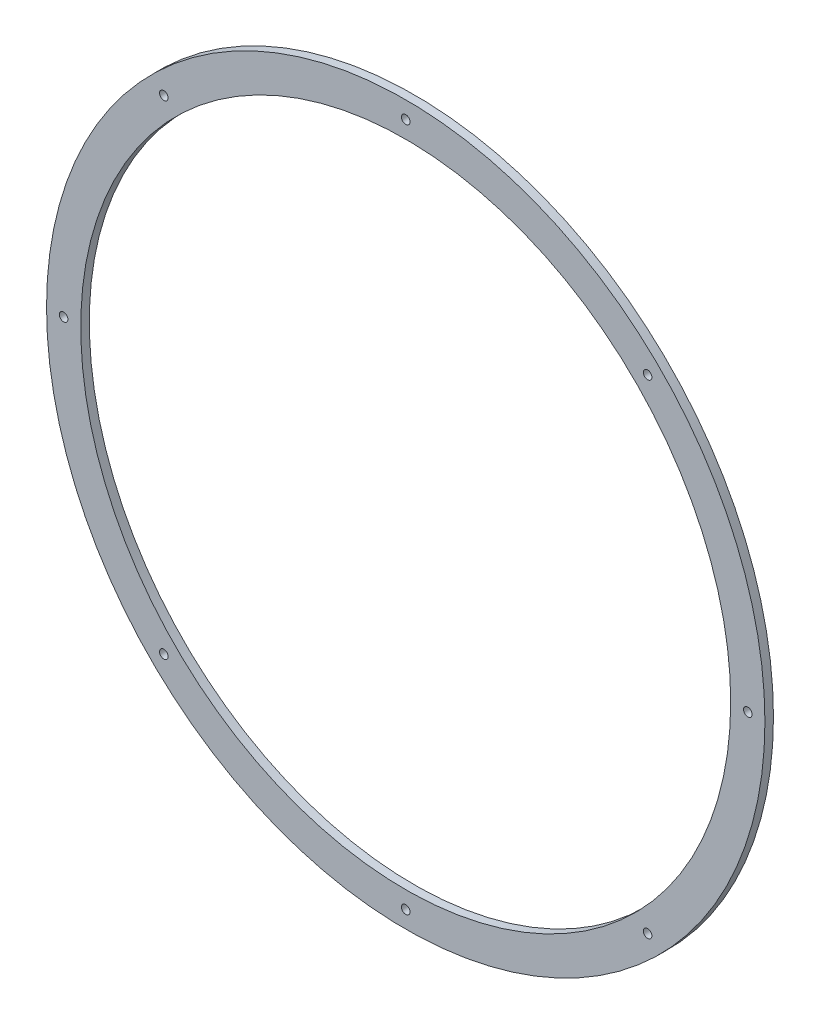
SolidWorks part; units mm, degrees
material "6061 Alloy"
ref_plane "Front Plane" through (0, 0, 0) normal (0, 0, 1) x (1, 0, 0)
ref_plane "Top Plane" through (0, 0, 0) normal (0, 1, 0) x (1, 0, 0)
ref_plane "Right Plane" through (0, 0, 0) normal (1, 0, 0) x (0, 0, -1)
sketch "Sketch1" plane through (0, 0, 0) normal (0, 0, 1) x (1, 0, 0)
  circle A0 centre (0, 0) radius 190
  circle A1 centre (0, 0) radius 210
  dimension "D1" = 380
  dimension "D2" = 20
extrude "Boss-Extrude1" add sketch "Sketch1" along normal blind 5
hole_wizard "M6 Tapped Hole1" positions "Sketch2" profile "Sketch3" tap size "M6" standard "ISO" end condition through all
sketch "Sketch2" plane through (0, 0, 5) normal (0, 0, 1) x (1, 0, 0)
  line L0 (0, 0) -> (0, 200) construction
  line L2 (0, 200) -> (0, 210) construction
  circle A0 centre (0, 0) radius 210 construction
  point P0 (0, 200)
  dimension "D1" = 10
sketch "Sketch3" plane through (0, 200, 5) normal (1, 0, 0) x (0, -1, 0)
  line L0 (0, 0) -> (0, 5)
  line L1 (0, 5) -> (2.5, 5)
  line L2 (2.5, 5) -> (2.5, 0)
  line L5 (2.5, 0) -> (0, 0)
  line L11 (0, -6.35) -> (0, 107.95) construction
  dimension "Thru Tap Drill Dia." = 5
  dimension "Thru Tap Drill Depth" = 5
cosmetic thread "Hole Thread1" parameters "D2"=6
pattern_circular "CirPattern1" count 8 over 360 about axis through (0, 0, 0) along (0, 0, 1) of "M6 Tapped Hole1"
cosmetic thread "Hole Thread2" parameters "D2"=6
cosmetic thread "Hole Thread3" parameters "D2"=6
cosmetic thread "Hole Thread4" parameters "D2"=6
cosmetic thread "Hole Thread5" parameters "D2"=6
cosmetic thread "Hole Thread6" parameters "D2"=6
cosmetic thread "Hole Thread7" parameters "D2"=6
cosmetic thread "Hole Thread8" parameters "D2"=6
